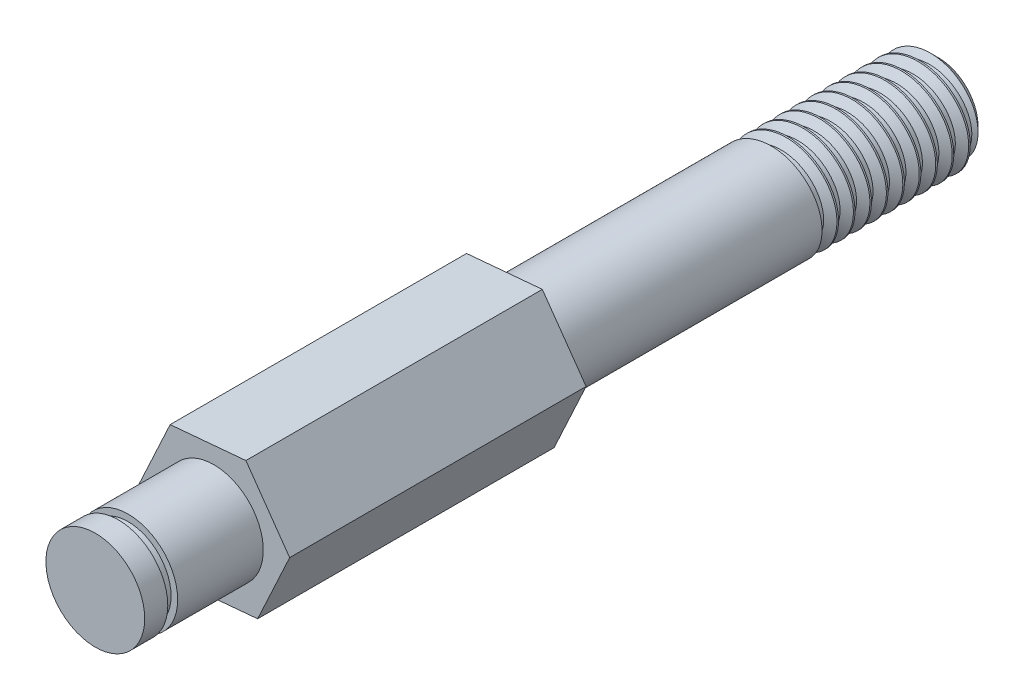
SolidWorks part; units mm, degrees
ref_plane "前视基准面" through (0, 0, 0) normal (0, 0, 1) x (1, 0, 0)
ref_plane "上视基准面" through (0, 0, 0) normal (0, 1, 0) x (1, 0, 0)
ref_plane "右视基准面" through (0, 0, 0) normal (1, 0, 0) x (0, 0, -1)
sketch "草图1" plane through (0, 0, 0) normal (0, 0, 1) x (1, 0, 0)
  circle A0 centre (0, 0) radius 1.5
  dimension "D1" = 3
extrude "凸台-拉伸1" add sketch "草图1" along normal blind 3.6
sketch "草图2" plane through (0, 0, 0) normal (0, 0, -1) x (-1, 0, 0)
  line L1 (2.3002, -0.2059) -> (1.3284, 1.8891)
  line L2 (1.3284, 1.8891) -> (-0.9718, 2.095)
  line L3 (-0.9718, 2.095) -> (-2.3002, 0.2059)
  line L4 (-2.3002, 0.2059) -> (-1.3284, -1.8891)
  line L5 (-1.3284, -1.8891) -> (0.9718, -2.095)
  line L6 (0.9718, -2.095) -> (2.3002, -0.2059)
  circle A0 centre (0, 0) radius 2 construction
  dimension "D1" = 4
extrude "凸台-拉伸2" add sketch "草图2" along normal blind 9
sketch "草图3" plane through (0, 0, -9) normal (0, 0, -1) x (-1, 0, 0)
  circle A0 centre (0, 0) radius 1.5
  dimension "D1" = 3
extrude "凸台-拉伸3" add sketch "草图3" along normal blind 13
ref_plane "基准面1" through (0, 0, 2.6) normal (0, 0, 1) x (1, 0, 0)
sketch "草图4" plane through (0, 0, 2.6) normal (0, 0, 1) x (1, 0, 0)
  circle A0 centre (0, 0) radius 1.5 construction
  circle A1 centre (0, 0) radius 1.5
  circle A2 centre (0, 0) radius 1.3
  dimension "D1" = 2.6
extrude "切除-拉伸1" cut sketch "草图4" along normal blind 0.3
chamfer "倒角1" distance 0.3 angle 45 1 edges at (-1.5, 0, -22)
sketch "草图5" plane through (0, 0, -22) normal (0, 0, -1) x (-1, 0, 0)
  circle A0 centre (0, 0) radius 1.5
  dimension "D1" = 3
curve "螺旋线/涡状线1" pitch 0.5 height 5 turns 10
sketch "草图6" plane through (0, 0, 0) normal (0, 1, 0) x (1, 0, 0)
  line L0 (-1.6252, 21.6383) -> (-1.6252, 22.2383)
  line L1 (-1.6252, 22.2383) -> (-1.2452, 22.0133)
  line L2 (-1.2452, 22.0133) -> (-1.2452, 21.8633)
  line L3 (-1.2452, 21.8633) -> (-1.6252, 21.6383)
  line L4 (-1.3198, 21.9383) -> (-1.7926, 21.9383) construction
  dimension "D1" = 0.3
  dimension "D2" = 0.15
  dimension "D3" = 0.38
sweep "切除-扫描1" cut profiles "草图6" path "螺旋线/涡状线1"
